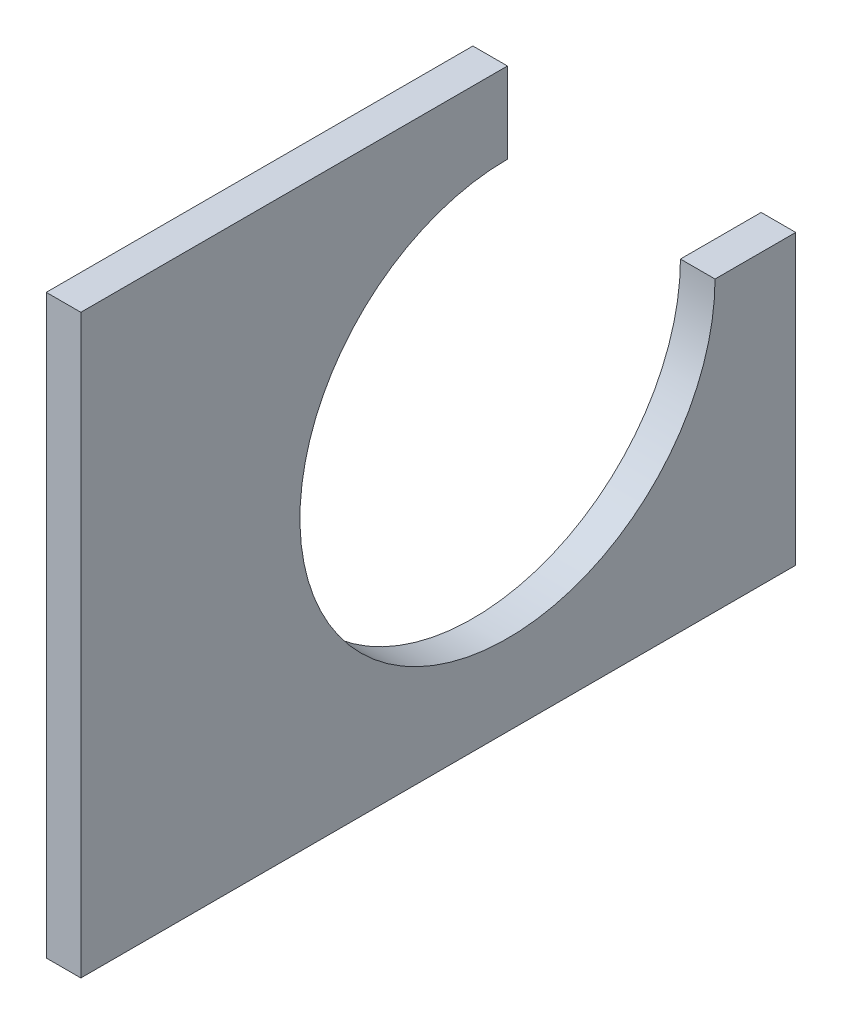
SolidWorks part; units mm, degrees
ref_plane "Front Plane" through (0, 0, 0) normal (0, 0, 1) x (1, 0, 0)
ref_plane "Top Plane" through (0, 0, 0) normal (0, 1, 0) x (1, 0, 0)
ref_plane "Right Plane" through (0, 0, 0) normal (1, 0, 0) x (0, 0, -1)
sketch "Sketch1" plane through (0, 0, 0) normal (1, 0, 0) x (0, 0, -1)
  line L0 (0, 25) -> (0, 18)
  line L1 (-37, 25) -> (0, 25)
  line L3 (-37, -25) -> (25, -25)
  line L5 (-40, 25) -> (40, -25) construction
  line L6 (-40, -25) -> (40, 25) construction
  line L7 (18, 0) -> (25, 0)
  line L9 (25, 0) -> (25, -25)
  line L10 (-37, 25) -> (-37, -25)
  arc A0 (0, 18) -> (18, 0) centre (0, 0) ccw
extrude "Boss-Extrude1" add sketch "Sketch1" along normal blind 3
